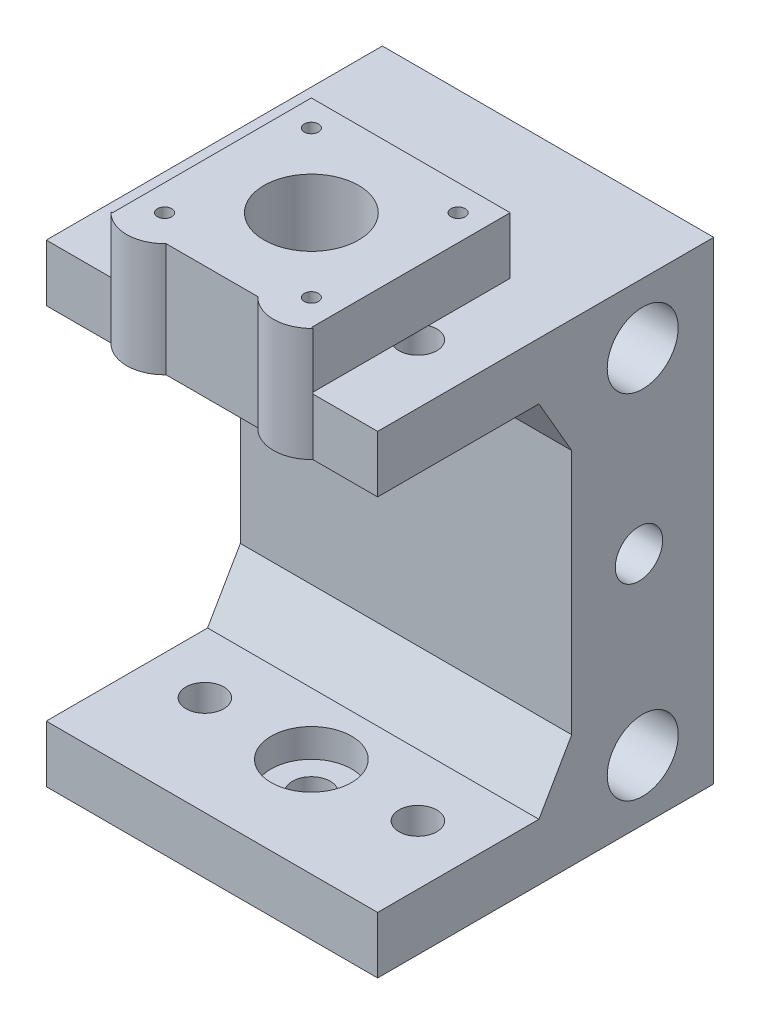
SolidWorks part; units mm, degrees
ref_plane "Front Plane" through (0, 0, 0) normal (0, 0, 1) x (1, 0, 0)
ref_plane "Top Plane" through (0, 0, 0) normal (0, 1, 0) x (1, 0, 0)
ref_plane "Right Plane" through (0, 0, 0) normal (1, 0, 0) x (0, 0, -1)
sketch "Sketch1" plane through (0, 0, 0) normal (1, 0, 0) x (0, 0, -1)
  line L0 (30, 50) -> (30, -50)
  line L1 (30, -50) -> (-41, -50)
  line L2 (-41, -50) -> (-41, -38)
  line L3 (-41, -38) -> (0, -38)
  line L4 (0, -38) -> (0, 38)
  line L6 (0, 0) -> (30, 0) construction
  line L7 (-41, 38) -> (0, 38)
  line L8 (-41, 50) -> (-41, 38)
  line L9 (30, 50) -> (-41, 50)
  dimension "D1" = 100
  dimension "D2" = 12
  dimension "D3" = 30
  dimension "D4" = 41
extrude "Boss-Extrude1" add sketch "Sketch1" along normal mid plane 70
sketch "Sketch2" plane through (0, 50, 0) normal (0, 1, 0) x (1, 0, 0)
  line L0 (0, 30) -> (0, -41) construction
  line L1 (35, 30) -> (-35, 30) construction
  line L2 (35, -41) -> (-35, -41) construction
  line L3 (35, 0) -> (-35, 0) construction
  line L4 (35, 30) -> (35, -41) construction
  line L5 (-35, 30) -> (-35, -41) construction
  circle A0 centre (-22.5, -20) radius 4
  circle A1 centre (22.5, -20) radius 4
  circle A2 centre (0, -20) radius 4
  dimension "D1" = 8
  dimension "D2" = 45
  dimension "D3" = 20
extrude "Cut-Extrude1" cut sketch "Sketch2" against normal through all
sketch "Sketch3" plane through (35, 0, 0) normal (1, 0, 0) x (0, 0, -1)
  line L0 (0, 0) -> (30, 0) construction
  line L1 (30, -50) -> (30, 50) construction
  circle A0 centre (15, -37.25) radius 7.5
  circle A1 centre (15, 37.25) radius 7.5
  circle A2 centre (14.2, 0) radius 5
  point P8 (15, 0)
  dimension "D1" = 15
  dimension "D3" = 10
  dimension "D2" = 74.5
  dimension "D4" = 0.8
extrude "Cut-Extrude2" cut sketch "Sketch3" against normal through all and the other way through all
chamfer "Chamfer1" distance 12 angle 30 1 edges at (0, -38, 0)
chamfer "Chamfer2" distance 12 angle 30 1 edges at (0, 38, 0)
sketch "Sketch4" plane through (0, 50, 0) normal (0, 1, 0) x (1, 0, 0)
  circle A0 centre (0, -20) radius 10
  dimension "D1" = 20
extrude "Cut-Extrude3" cut sketch "Sketch4" against normal up to surface (12 mm away) up to face at (-22.5, 38, 24)
sketch "Sketch5" plane through (0, 50, 0) normal (0, 1, 0) x (1, 0, 0)
  circle A1 centre (15.5, -4.5) radius 1.5
  circle A2 centre (15.5, -4.5) radius 1.5
  circle A3 centre (-15.5, -4.5) radius 1.5
  circle A4 centre (-15.5, -4.5) radius 1.5
  circle A5 centre (15.5, -35.5) radius 1.5
  circle A6 centre (15.5, -35.5) radius 1.5
  circle A7 centre (-15.5, -35.5) radius 1.5
  circle A8 centre (-15.5, -35.5) radius 1.5
  dimension "D1" = 0
  dimension "D2" = 0
  dimension "D3" = 0
  dimension "D4" = 0
extrude "Cut-Extrude4" cut sketch "Sketch5" against normal up to vertex (12 mm away)
sketch "Sketch6" plane through (0, 50, 0) normal (0, 1, 0) x (1, 0, 0)
  line L0 (35, -41) -> (-35, -41) construction
  line L1 (-21.3095, -41) -> (-9.6905, -41)
  line L2 (0, -39.05) -> (0, 39.05) construction
  line L3 (21.3095, -41) -> (9.6905, -41)
  arc A0 (-21.3095, -41) -> (-9.6905, -41) centre (-15.5, -35.5) ccw
  arc A1 (21.3095, -41) -> (9.6905, -41) centre (15.5, -35.5) cw
  dimension "D1" = 8
extrude "Boss-Extrude2" add sketch "Sketch6" against normal mid plane 24
sketch "Sketch7" plane through (0, 0, 0) normal (0, 1, 0) x (1, 0, 0)
  line L0 (0, 0) -> (0, -20) construction
  line L1 (0, -20) -> (35, -20) construction
  line L2 (35, -41) -> (35, -6.9282) construction
  circle A2 centre (15.5, -4.5) radius 1.5 construction
  circle A8 centre (15.5, -4.5) radius 2.75
  circle A9 centre (-15.5, -4.5) radius 2.75
  circle A10 centre (15.5, -35.5) radius 2.75
  circle A11 centre (-15.5, -35.5) radius 2.75
  point P13 (15.5, -4.5)
  point P14 (15.5, -35.5)
  point P15 (-15.5, -35.5)
  point P16 (-15.5, -4.5)
  dimension "D1" = 5.5
extrude "Cut-Extrude5" cut sketch "Sketch7" along normal offset from surface (41 mm away) 9 up to face at (-15.5, 50, 6)
sketch "Sketch8" plane through (0, 50, 0) normal (0, 1, 0) x (1, 0, 0)
  line L16 (-17.4645, 1) -> (-21, -2.5355)
  line L17 (17.4645, 1) -> (-17.4645, 1)
  line L18 (21, -2.5355) -> (17.4645, 1)
  line L19 (21, -37.4645) -> (21, -2.5355)
  line L20 (17.4645, -41) -> (21, -37.4645)
  line L21 (-17.4645, -41) -> (17.4645, -41)
  line L22 (-21, -37.4645) -> (-17.4645, -41)
  line L23 (-21, -2.5355) -> (-21, -37.4645)
  line L25 (17.4645, 1) -> (-17.4645, 1)
  line L27 (21, -37.4645) -> (21, -2.5355)
  line L29 (-17.4645, -41) -> (17.4645, -41)
  line L31 (-21, -2.5355) -> (-21, -37.4645)
  line L32 (-21, -2.5355) -> (-21, 1)
  line L33 (-21, 1) -> (-17.4645, 1)
  line L34 (17.4645, 1) -> (21, 1)
  line L35 (21, 1) -> (21, -2.5355)
  line L36 (21, -37.4645) -> (21, -41)
  line L37 (9.6905, -41) -> (21.3095, -41) construction
  line L38 (21, -41) -> (17.4645, -41)
  line L39 (-17.4645, -41) -> (-21, -41)
  line L40 (-21.3095, -41) -> (-9.6905, -41) construction
  line L41 (-21, -41) -> (-21, -37.4645)
  circle A0 centre (0, -20) radius 10 construction
  circle A1 centre (0, -20) radius 10
  circle A2 centre (-15.5, -35.5) radius 1.5 construction
  circle A3 centre (15.5, -35.5) radius 1.5 construction
  circle A4 centre (-15.5, -4.5) radius 1.5 construction
  circle A5 centre (15.5, -4.5) radius 1.5 construction
  circle A6 centre (-15.5, -35.5) radius 1.5
  circle A7 centre (15.5, -35.5) radius 1.5
  circle A8 centre (-15.5, -4.5) radius 1.5
  circle A9 centre (15.5, -4.5) radius 1.5
  dimension "D1" = 0
extrude "Boss-Extrude3" add sketch "Sketch8" along normal blind 12
sketch "Sketch9" plane through (0, -38, 0) normal (0, 1, 0) x (1, 0, 0)
  circle A0 centre (0, -20) radius 8.5
  dimension "D1" = 17
extrude "Cut-Extrude6" cut sketch "Sketch9" against normal blind 6
sketch "Sketch10" plane through (-35, 0, 0) normal (-1, 0, 0) x (0, 0, 1)
  circle A0 centre (-14.2, 0) radius 11
  dimension "D1" = 22
extrude "Cut-Extrude7" cut sketch "Sketch10" against normal blind 4
sketch "Sketch11" plane through (-31, 0, 0) normal (-1, 0, 0) x (0, 0, 1)
  line L1 (-14.2, 0) -> (-6.2, 0) construction
  circle A1 centre (-14.2, 0) radius 5 construction
  circle A2 centre (-14.2, 0) radius 5
  circle A6 centre (-14.2, 8) radius 1.1
  circle A7 centre (-6.2, 0) radius 1.1
  circle A8 centre (-14.2, -8) radius 1.1
  circle A9 centre (-22.2, 0) radius 1.1
  dimension "D3" = 4
  dimension "D1" = 2.2
  dimension "D2" = 8
extrude "Cut-Extrude8" cut sketch "Sketch11" against normal blind 20
